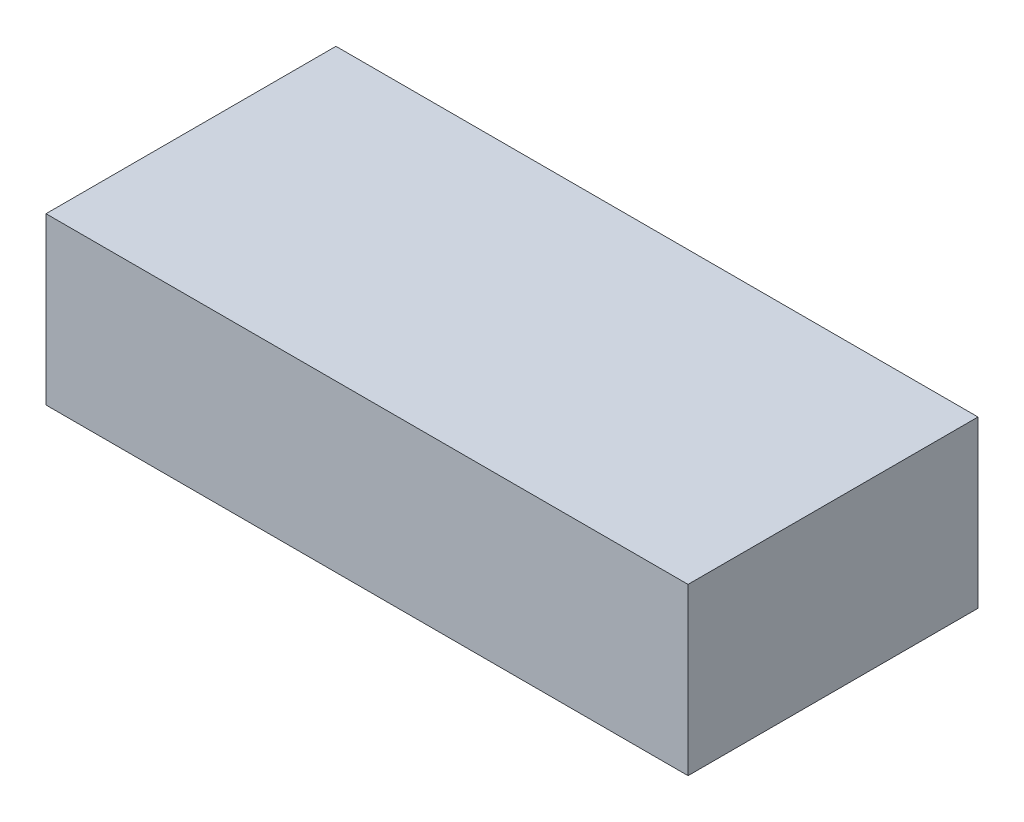
SolidWorks part; units mm, degrees
ref_plane "Front Plane" through (0, 0, 0) normal (0, 0, 1) x (1, 0, 0)
ref_plane "Top Plane" through (0, 0, 0) normal (0, 1, 0) x (1, 0, 0)
ref_plane "Right Plane" through (0, 0, 0) normal (1, 0, 0) x (0, 0, -1)
sketch "Sketch1" plane through (0, 0, 0) normal (0, 1, 0) x (1, 0, 0)
  line L1 (-98.425, -44.45) -> (98.425, -44.45)
  line L2 (-98.425, -44.45) -> (-98.425, 44.45)
  line L3 (-98.425, 44.45) -> (98.425, 44.45)
  line L4 (98.425, -44.45) -> (98.425, 44.45)
  line L5 (-98.425, -44.45) -> (98.425, 44.45) construction
  line L6 (-98.425, 44.45) -> (98.425, -44.45) construction
  point P0 (0, 0)
  dimension "D1" = 196.85
  dimension "D2" = 88.9
extrude "Boss-Extrude1" add sketch "Sketch1" along normal mid plane 50.8
